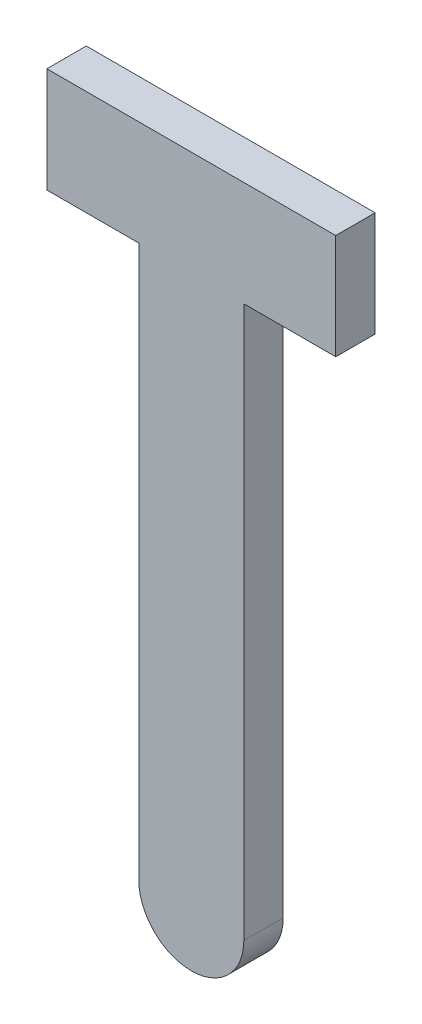
SolidWorks part; units mm, degrees
ref_plane "Face" through (0, 0, 0) normal (0, 0, 1) x (1, 0, 0)
ref_plane "Dessus" through (0, 0, 0) normal (0, 1, 0) x (1, 0, 0)
ref_plane "Droite" through (0, 0, 0) normal (1, 0, 0) x (0, 0, -1)
sketch "Esquisse1" plane through (0, 0, 0) normal (0, 0, 1) x (1, 0, 0)
  line L0 (-5.5, 0) -> (5.5, 0)
  line L1 (-5.5, -4) -> (-2, -4)
  line L2 (0, 0) -> (0, -33.6958) construction
  line L3 (-5.5, 0) -> (-5.5, -4)
  line L5 (5.5, -4) -> (5.5, 0)
  line L6 (2, -4) -> (5.5, -4)
  line L8 (-2, -4) -> (-2, -25)
  line L10 (2, -4) -> (2, -25)
  arc A0 (-2, -25) -> (2, -25) centre (0, -25) ccw
  dimension "D5" = 25
  dimension "D1" = 4
  dimension "D2" = 11
  dimension "D3" = 4
  dimension "D4" = 3.5
  dimension "D6" = 11
extrude "Extrusion1" add sketch "Esquisse1" along normal blind 1.5
